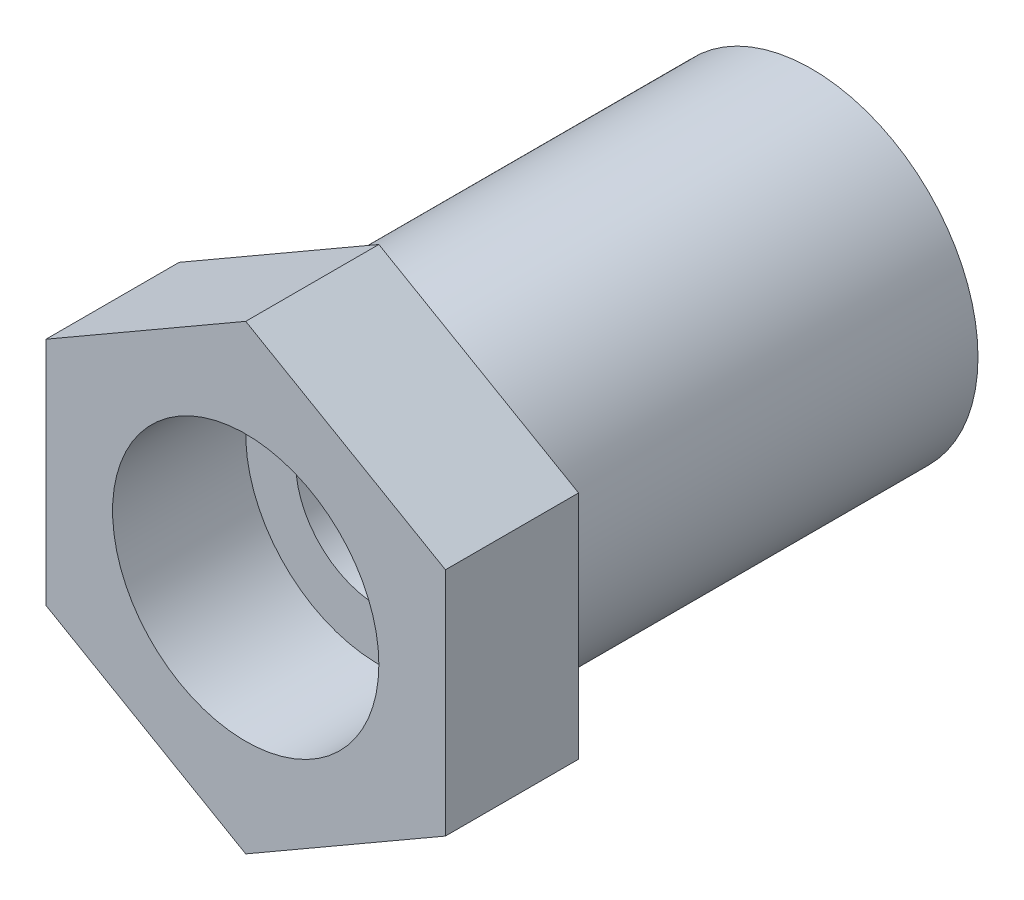
SolidWorks part; units mm, degrees
ref_plane "Front Plane" through (0, 0, 0) normal (0, 0, 1) x (1, 0, 0)
ref_plane "Top Plane" through (0, 0, 0) normal (0, 1, 0) x (1, 0, 0)
ref_plane "Right Plane" through (0, 0, 0) normal (1, 0, 0) x (0, 0, -1)
sketch "Sketch2" plane through (0, 0, 0) normal (0, 0, 1) x (1, 0, 0)
  circle A0 centre (-29.0609, 5.3372) radius 5
extrude "Boss-Extrude1" add sketch "Sketch2" along normal blind 13
sketch "Sketch3" plane through (0, 0, 13) normal (0, 0, 1) x (1, 0, 0)
  line L1 (-29.0609, -1.591) -> (-23.0609, 1.8731)
  line L2 (-23.0609, 1.8731) -> (-23.0609, 8.8013)
  line L3 (-23.0609, 8.8013) -> (-29.0609, 12.2654)
  line L4 (-29.0609, 12.2654) -> (-35.0609, 8.8013)
  line L5 (-35.0609, 8.8013) -> (-35.0609, 1.8731)
  line L6 (-35.0609, 1.8731) -> (-29.0609, -1.591)
  circle A0 centre (-29.0609, 5.3372) radius 6 construction
  dimension "D1" = 12
extrude "Boss-Extrude2" add sketch "Sketch3" along normal blind 4 contours L3 L4 L5 L6 L1 L2
sketch "Sketch4" plane through (0, 0, 0) normal (0, 0, -1) x (-1, 0, 0)
  circle A0 centre (29.0609, 5.3372) radius 2.5
extrude "Cut-Extrude1" cut sketch "Sketch4" against normal blind 13
sketch "Sketch5" plane through (0, 0, 17) normal (0, 0, 1) x (1, 0, 0)
  circle A0 centre (-29.0609, 5.3372) radius 4
extrude "Cut-Extrude2" cut sketch "Sketch5" against normal blind 4
